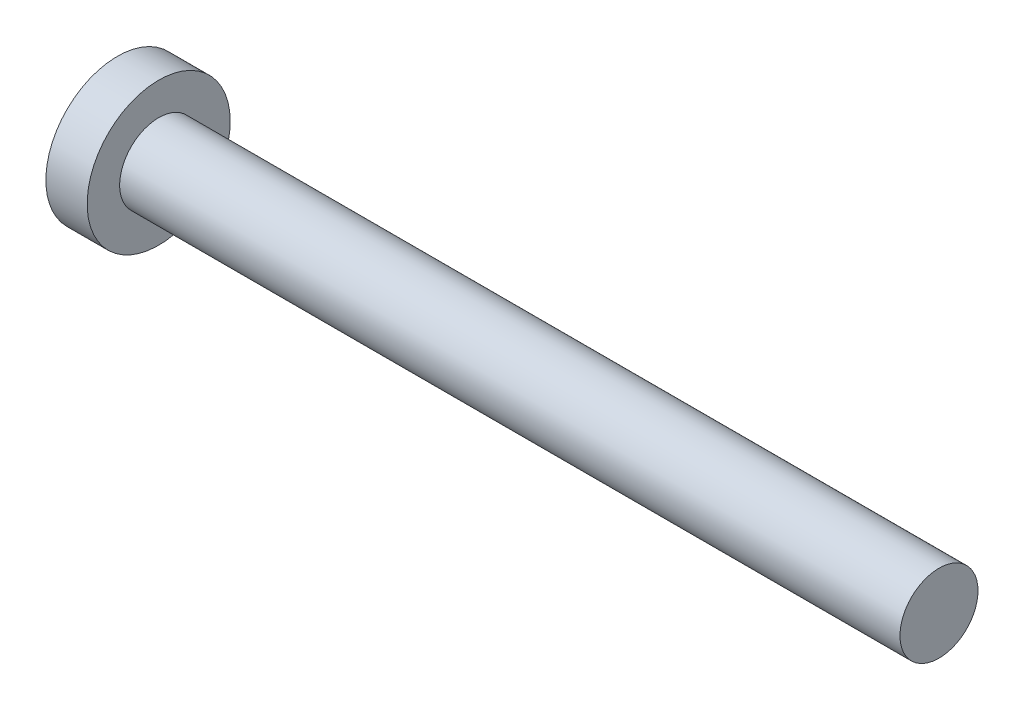
SolidWorks part; units mm, degrees
ref_plane "Front" through (0, 0, 0) normal (0, 0, 1) x (1, 0, 0)
ref_plane "Top" through (0, 0, 0) normal (0, 1, 0) x (1, 0, 0)
ref_plane "Right" through (0, 0, 0) normal (1, 0, 0) x (0, 0, -1)
other "Configuration Table"
sketch "Sketch1" plane through (0, 0, 0) normal (0, 0, 1) x (1, 0, 0)
  line L0 (32.15, 1.5) -> (3.15, 1.5)
  line L1 (2.15, 1.8) -> (2.15, 2.75)
  line L2 (2.15, 2.75) -> (0.5628, 2.75)
  line L3 (3.15, 1.5) -> (2.45, 1.5) construction
  line L4 (32.15, 1.5) -> (32.15, 0)
  line L5 (4.5158, 0) -> (-13.5157, 0) construction
  line L6 (32.15, 0) -> (0, 0)
  line L7 (3.15, 1.5) -> (2.15, 1.5)
  line L8 (2.15, 1.5) -> (2.15, 1.8)
  arc A0 (0.5628, 2.75) -> (0, 0) centre (7, 0) ccw
  arc A1 (2.15, 1.8) -> (2.45, 1.5) centre (2.45, 1.8) ccw construction
  dimension "D1" = 0.3
  dimension "r1" = 7
  dimension "d" = 3
  dimension "dk" = 5.5
  dimension "l" = 30
  dimension "k" = 2.15
  dimension "a" = 1
  dimension "da" = 3.6
revolve "Base" add sketch "Sketch1" angle 360 about L5
cosmetic thread "ThreadCosmetic1" [suppressed] parameters "bb"=30, "THD_MINOR"=2.459
sketch "Sketch6" plane through (0, 0, 0) normal (1, 0, 0) x (0, 0, -1)
  line L0 (-1.9271, 0) -> (2.0512, 0) construction
  line L1 (0, 1.8651) -> (0, -2.0207) construction
  line L2 (0.35, 0.35) -> (0.35, 1.75)
  line L3 (0.35, 1.75) -> (-0.35, 1.75)
  line L4 (-0.35, 0.35) -> (-0.35, 1.75)
  line L5 (0.35, 0.35) -> (1.75, 0.35)
  line L6 (1.75, 0.35) -> (1.75, -0.35)
  line L7 (-1.75, 0.35) -> (-1.75, -0.35)
  line L8 (-0.35, 0.35) -> (-1.75, 0.35)
  line L9 (-0.35, -0.35) -> (-1.75, -0.35)
  line L10 (0.35, -0.35) -> (1.75, -0.35)
  line L11 (-0.35, -0.35) -> (-0.35, -1.75)
  line L12 (0.35, -1.75) -> (-0.35, -1.75)
  line L13 (0.35, -0.35) -> (0.35, -1.75)
  point P16 (-1.75, 0)
  point P17 (1.75, 0)
extrude "Cut-Extrude2" cut sketch "Sketch6" along normal blind 1.43
fillet "Fillet5" radius 0.3 4 edges at (0.7238, -0.35, 0.35) (0.7238, -0.35, -0.35) (0.7238, 0.35, 0.35) (0.7238, 0.35, -0.35)
draft "Draft2" type of draft neutral plane draft angle 30 neutral plane "Right" faces to draft 4 face at (0.8284, 0, 1.75) face at (0.8284, 1.75, 0) face at (0.8284, -1.75, 0) face at (0.8284, 0, -1.75) neutral plane through (0, 0, 0) neutral plane normal (1, 0, 0) reverse direction yes parameters "D1"=30
sketch "Sketch8" plane through (0, 0, 0) normal (0, 0, 1) x (1, 0, 0)
  line L0 (7.15, 1.5) -> (5.9, 1.2295)
  line L1 (5.9, 1.2295) -> (2.15, 1.2295)
  line L2 (32.15, -1.5) -> (32.15, 1.5) construction
  line L3 (2.15, -2.75) -> (2.15, 2.75) construction
  line L6 (2.15, 1.2295) -> (2.15, 2.75)
  line L7 (2.15, 2.75) -> (7.15, 2.75)
  line L8 (7.15, 2.75) -> (7.15, 1.5)
  line L9 (69.9753, 0) -> (60.4594, 0) construction
  dimension "x" = 1.25
  dimension "d" = 3
  dimension "THD_MINOR" = 2.459
  dimension "b" = 25
sketch "Sketch10" plane through (0, 0, 0) normal (0, 0, 1) x (1, 0, 0)
  line L0 (32.15, 1.2657) -> (32.2852, 1.5)
  line L1 (32.2852, 1.5) -> (32.2852, 1.7705)
  line L2 (32.2852, 1.7705) -> (32.0147, 1.7705)
  line L3 (32.0147, 1.7705) -> (32.0147, 1.5)
  line L4 (32.0147, 1.5) -> (32.15, 1.2657)
  line L5 (0, 0) -> (78.5832, 0) construction
  line L6 (32.15, -1.5) -> (32.15, 1.5) construction
  dimension "D1" = 3
  dimension "D2" = 0.2705
revolve "Cut-Revolve10" [suppressed] cut sketch "Sketch10" angle 360 about L5
pattern_linear "LPattern10" [suppressed] count 92 spacing 0.3246 along (1, 0, 0)
equation "\"D1@Sketch6\" = \"m@Sketch6\" / 5"
equation "\"D1@Sketch10\" = \"d@Sketch1\""
equation "\"D2@Sketch10\" =  ( \"d@Sketch1\" - \"THD_MINOR@ThreadCosmetic1\" )  / 2"
equation "\"D3@LPattern10\" = \"D2@Sketch10\" * 1.2"
equation "\"D1@LPattern10\" = \"bb@ThreadCosmetic1\" / \"D3@LPattern10\" "
